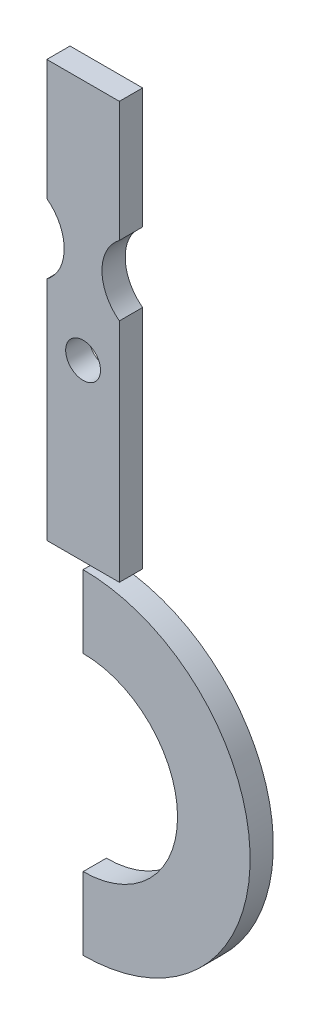
SolidWorks part; units mm, degrees
material "1.0577 (S355J2G4)"
ref_plane "Front Plane" through (0, 0, 0) normal (0, 0, 1) x (1, 0, 0)
ref_plane "Top Plane" through (0, 0, 0) normal (0, 1, 0) x (1, 0, 0)
ref_plane "Right Plane" through (0, 0, 0) normal (1, 0, 0) x (0, 0, -1)
sketch "Sketch1" plane through (0, 0, 0) normal (0, 0, 1) x (1, 0, 0)
  line L0 (-12.5, -13.6382) -> (-12.5, -23)
  line L1 (12.5, -13.6382) -> (12.5, -23)
  line L2 (0, 0) -> (0, -1238.5) construction
  line L3 (-12.5, -47) -> (-12.5, -125)
  line L4 (12.5, -47) -> (12.5, -125)
  line L5 (0, -152.4567) -> (-12.5, -152.4567) construction
  line L6 (15.2393, -240.4887) -> (11.4444, -215.4646) construction
  line L7 (0, -127.4567) -> (0, -152.4567)
  line L8 (-12.5, -13) -> (12.5, -13) construction
  line L9 (12.5, -57) -> (-12.5, -57) construction
  line L10 (-12.5, -13.6382) -> (-12.5, 18.5)
  line L11 (0, 18.5) -> (-21.151, 18.5) construction
  line L12 (-12.5, 18.5) -> (12.5, 18.5)
  line L13 (12.5, 18.5) -> (12.5, -13.6382)
  line L14 (12.5, -125) -> (-12.5, -125)
  line L15 (-12.5, -152.4567) -> (-12.5, -154.9531)
  line L16 (-12.5, -125) -> (-12.5, -152.4567) construction
  line L17 (32.5433, -185) -> (57.5433, -185)
  line L18 (0, -242.5433) -> (0, -217.5433)
  circle A0 centre (0, 0) radius 8.5 construction
  arc A1 (-12.5, -13.6382) -> (12.5, -13.6382) centre (0, 0) cw construction
  arc A2 (-12.5, -23) -> (-12.5, -47) centre (-21.5, -35) cw
  arc A3 (12.5, -23) -> (12.5, -47) centre (21.5, -35) ccw
  arc A4 (0, -152.4567) -> (0, -217.5433) centre (0, -185) cw
  arc A5 (11.4444, -215.4646) -> (0, -211.5) centre (0, -230) ccw construction
  arc A6 (0, -242.5433) -> (0, -127.4567) centre (0, -185) ccw
  arc A7 (8.462, -229.1972) -> (0, -221.5) centre (0, -230) ccw construction
  arc A8 (0, -230) -> (0, -140) centre (0, -185) ccw construction
  circle A9 centre (0, -65) radius 6
  arc A10 (-12.5, -154.9531) -> (0, -152.4567) centre (0, -185) cw construction
  arc A11 (32.5433, -185) -> (11.4444, -215.4646) centre (0, -185) cw construction
  arc A12 (15.2393, -240.4887) -> (57.5433, -185) centre (0, -185) ccw construction
  arc A13 (0, -238.5) -> (8.462, -229.1972) centre (0, -230) ccw construction
  arc A14 (0, -221.5) -> (0, -238.5) centre (0, -230) ccw construction
  arc A15 (0, -211.5) -> (0, -248.5) centre (0, -230) ccw construction
  arc A16 (0, -248.5) -> (15.2393, -240.4887) centre (0, -230) ccw construction
  point P11 (-6.5, -35)
  point P21 (13.3418, -227.9767)
  point P25 (6.5, -35)
  dimension "D1" = 17
  dimension "D2" = 10
  dimension "D3" = 17
  dimension "D4" = 25
  dimension "D7" = 230
  dimension "D9" = 10
  dimension "D11" = 15
  dimension "D12" = 185
  dimension "D13" = 12
  dimension "D10" = 65
  dimension "D5" = 13
  dimension "D6" = 25
  dimension "D8" = 35
  dimension "D14" = 9
  dimension "D15" = 24
  dimension "D16" = 10
  dimension "D17" = 10
  dimension "D18" = 60
extrude "Boss-Extrude1" add sketch "Sketch1" along normal blind 8 contours A5 A6 L4 A3 L1 A1 L0 A2 L3 L5 A4 A7 A0 | L17 A6 L7 A4 | L18 A6 L17 A4
sketch "Sketch2" plane through (0, 0, 8) normal (0, 0, 1) x (1, 0, 0)
  line L0 (-12.5, -95) -> (-11, -92.4)
  line L1 (-12.5, -47) -> (-12.5, -125) construction
  line L2 (-11, -92.4) -> (-11, -99.5)
  line L3 (-11, -99.5) -> (-10.5, -100)
  line L4 (-10.5, -100) -> (-4.1667, -100)
  line L7 (-10.5, -100) -> (-11, -100.5)
  line L8 (-11, -100.5) -> (-11, -107.6)
  line L9 (-11, -107.6) -> (-12.5, -105)
  line M16 (-12.5, -47) -> (-12.5, -125)
  dimension "D1" = 10
  dimension "D2" = 1.5
  dimension "D3" = 2
  dimension "D4" = 1
  dimension "D5" = 7.6
  dimension "D6" = 8.3333
  dimension "D7" = 100
extrude "Cut-Extrude1" [suppressed] cut sketch "Sketch2" against normal through all contours L9 L8 L7 L3 L2 L0 M16
